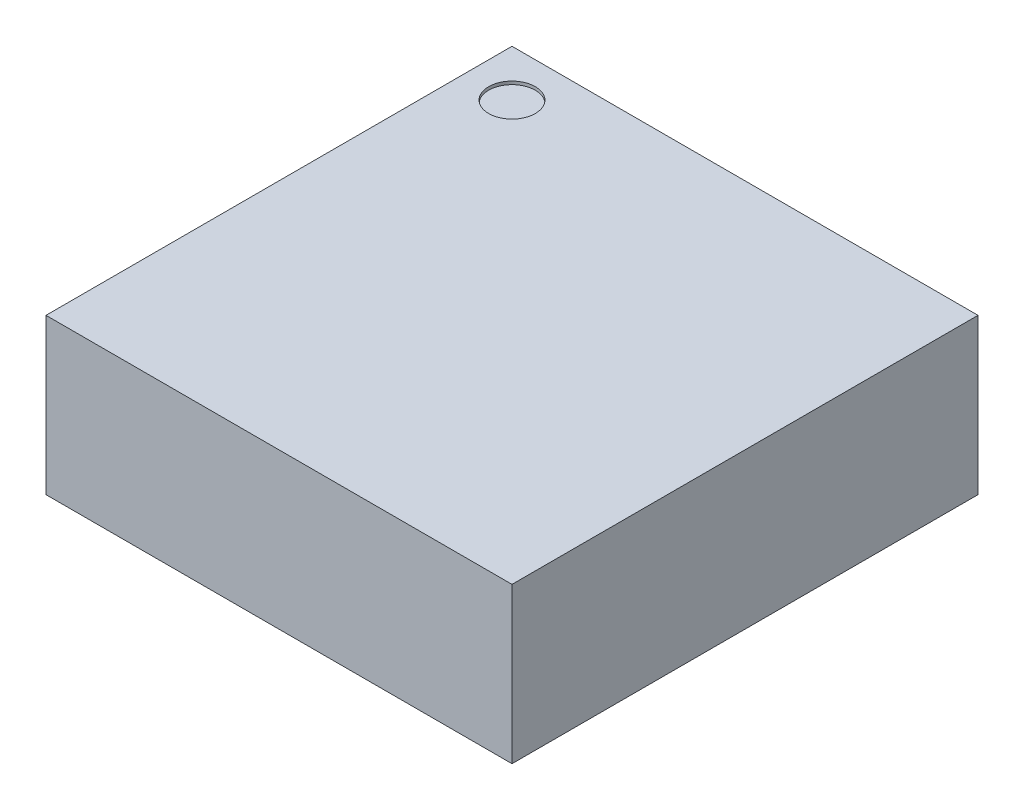
SolidWorks part; units mm, degrees
ref_plane "Front Plane" through (0, 0, 0) normal (0, 0, 1) x (1, 0, 0)
ref_plane "Top Plane" through (0, 0, 0) normal (0, 1, 0) x (1, 0, 0)
ref_plane "Right Plane" through (0, 0, 0) normal (1, 0, 0) x (0, 0, -1)
sketch "Sketch1" plane through (0, 0, 0) normal (0, 1, 0) x (1, 0, 0)
  line L0 (1.5, -1.5) -> (-1.5, 1.5) construction
  line L1 (-1.5, -1.5) -> (1.5, -1.5)
  line L2 (-1.5, -1.5) -> (-1.5, 1.5)
  line L3 (-1.5, 1.5) -> (1.5, 1.5)
  line L4 (1.5, -1.5) -> (1.5, 1.5)
  dimension "D1" = 3
extrude "Boss-Extrude1" add sketch "Sketch1" along normal blind 1
sketch "Sketch2" plane through (0, 0, 0) normal (0, -1, 0) x (1, 0, 0)
  line L0 (1.5, -1.5) -> (-1.5, -1.5) construction
  line L1 (-0.6, 1.39) -> (-0.4, 1.39)
  line L2 (-0.65, 1.34) -> (-0.65, 0.98)
  line L3 (-0.65, 0.98) -> (-0.35, 0.98) construction
  line L4 (-0.35, 1.34) -> (-0.35, 0.98)
  line L5 (-0.1, 1.39) -> (0.1, 1.39)
  line L6 (-0.15, 1.34) -> (-0.15, 0.98)
  line L7 (-0.15, 0.98) -> (0.15, 0.98) construction
  line L8 (0.15, 1.34) -> (0.15, 0.98)
  line L9 (0.4, 1.39) -> (0.6, 1.39)
  line L10 (0.35, 1.34) -> (0.35, 0.98)
  line L11 (0.35, 0.98) -> (0.65, 0.98) construction
  line L12 (0.65, 1.34) -> (0.65, 0.98)
  line L13 (0.35, -0.98) -> (0.65, -0.98) construction
  line L14 (0.35, -0.98) -> (0.35, -1.34)
  line L15 (0.4, -1.39) -> (0.6, -1.39)
  line L16 (0.65, -0.98) -> (0.65, -1.34)
  line L17 (-0.15, -0.98) -> (0.15, -0.98) construction
  line L18 (-0.15, -0.98) -> (-0.15, -1.34)
  line L19 (-0.1, -1.39) -> (0.1, -1.39)
  line L20 (0.15, -0.98) -> (0.15, -1.34)
  line L21 (-0.65, -0.98) -> (-0.35, -0.98) construction
  line L22 (-0.65, -0.98) -> (-0.65, -1.34)
  line L23 (-0.6, -1.39) -> (-0.4, -1.39)
  line L24 (-0.35, -0.98) -> (-0.35, -1.34)
  line L25 (-1.34, 1.15) -> (-0.98, 1.15)
  line L26 (-1.39, 1.1) -> (-1.39, 0.9)
  line L27 (-1.34, 0.85) -> (-0.98, 0.85)
  line L28 (-0.98, 1.15) -> (-0.98, 0.85) construction
  line L29 (-1.34, 0.65) -> (-0.98, 0.65)
  line L30 (-1.39, 0.6) -> (-1.39, 0.4)
  line L31 (-1.34, 0.35) -> (-0.98, 0.35)
  line L32 (-0.98, 0.65) -> (-0.98, 0.35) construction
  line L33 (-1.34, 0.15) -> (-0.98, 0.15)
  line L34 (-1.39, 0.1) -> (-1.39, -0.1)
  line L35 (-1.34, -0.15) -> (-0.98, -0.15)
  line L36 (-0.98, 0.15) -> (-0.98, -0.15) construction
  line L37 (-1.34, -0.35) -> (-0.98, -0.35)
  line L38 (-1.39, -0.4) -> (-1.39, -0.6)
  line L39 (-1.34, -0.65) -> (-0.98, -0.65)
  line L40 (-0.98, -0.35) -> (-0.98, -0.65) construction
  line L41 (-1.34, -0.85) -> (-0.98, -0.85)
  line L42 (-1.39, -0.9) -> (-1.39, -1.1)
  line L43 (-1.34, -1.15) -> (-0.98, -1.15)
  line L44 (-0.98, -0.85) -> (-0.98, -1.15) construction
  line L45 (0.98, -0.35) -> (1.34, -0.35)
  line L46 (0.98, -0.35) -> (0.98, -0.65) construction
  line L47 (0.98, -0.65) -> (1.34, -0.65)
  line L48 (1.39, -0.4) -> (1.39, -0.6)
  line L49 (0.98, -0.85) -> (1.34, -0.85)
  line L50 (0.98, -0.85) -> (0.98, -1.15) construction
  line L51 (0.98, -1.15) -> (1.34, -1.15)
  line L52 (1.39, -0.9) -> (1.39, -1.1)
  line L53 (0.98, 0.15) -> (1.34, 0.15)
  line L54 (0.98, 0.15) -> (0.98, -0.15) construction
  line L55 (0.98, -0.15) -> (1.34, -0.15)
  line L56 (1.39, 0.1) -> (1.39, -0.1)
  line L57 (0.98, 0.65) -> (1.34, 0.65)
  line L58 (0.98, 0.65) -> (0.98, 0.35) construction
  line L59 (0.98, 0.35) -> (1.34, 0.35)
  line L60 (1.39, 0.6) -> (1.39, 0.4)
  line L61 (0.98, 1.15) -> (1.34, 1.15)
  line L62 (0.98, 1.15) -> (0.98, 0.85) construction
  line L63 (0.98, 0.85) -> (1.34, 0.85)
  line L64 (1.39, 1.1) -> (1.39, 0.9)
  line L65 (-0.5, 1.39) -> (-0.5, 1.6137) construction
  line L66 (0, 1.39) -> (0, 1.6766) construction
  line L67 (0.5, 1.39) -> (0.5, 1.6137) construction
  line L68 (1.39, 1) -> (1.9436, 1) construction
  line L69 (1.39, 0.5) -> (1.7859, 0.5) construction
  line L70 (1.39, 0) -> (1.8465, 0) construction
  line L71 (1.39, -1) -> (1.6565, -1) construction
  line L72 (1.39, -0.5) -> (1.7859, -0.5) construction
  line L73 (0.5, -1.39) -> (0.5, -2.1383) construction
  line L74 (0, -1.39) -> (0, -1.3125) construction
  line L75 (-0.5, -1.39) -> (-0.5, -1.6285) construction
  line L76 (-1.39, -1) -> (-1.7444, -1) construction
  line L77 (-1.39, -0.5) -> (-1.9469, -0.5) construction
  line L78 (-1.39, 0) -> (-1.7147, 0) construction
  line L79 (-1.39, 0.5) -> (-1.63, 0.5) construction
  line L80 (-1.39, 1) -> (-1.63, 1) construction
  line L81 (-1.5, 1.5) -> (1.5, 1.5) construction
  line L82 (1.5, 1.5) -> (1.5, -1.5) construction
  line L83 (-1.5, -1.5) -> (-1.5, 1.5) construction
  line L84 (-0.98, -0.85) -> (-0.88, -0.85)
  line L85 (-0.83, -0.9) -> (-0.83, -1)
  line L86 (-0.83, -1) -> (-0.98, -1.15)
  line L87 (-0.83, -0.5) -> (-0.83, -0.85) construction
  arc A0 (-0.65, 0.98) -> (-0.35, 0.98) centre (-0.5, 0.98) ccw
  arc A1 (-0.15, 0.98) -> (0.15, 0.98) centre (0, 0.98) ccw
  arc A2 (0.35, 0.98) -> (0.65, 0.98) centre (0.5, 0.98) ccw
  arc A3 (0.98, 1.15) -> (0.98, 0.85) centre (0.98, 1) ccw
  arc A4 (0.98, 0.35) -> (0.98, 0.65) centre (0.98, 0.5) cw
  arc A5 (0.98, 0.15) -> (0.98, -0.15) centre (0.98, 0) ccw
  arc A6 (0.98, -1.15) -> (0.98, -0.85) centre (0.98, -1) cw
  arc A7 (0.98, -0.35) -> (0.98, -0.65) centre (0.98, -0.5) ccw
  arc A8 (0.35, -0.98) -> (0.65, -0.98) centre (0.5, -0.98) cw
  arc A9 (0.15, -0.98) -> (-0.15, -0.98) centre (0, -0.98) ccw
  arc A10 (-0.35, -0.98) -> (-0.65, -0.98) centre (-0.5, -0.98) ccw
  arc A11 (-0.88, -0.85) -> (-0.83, -0.9) centre (-0.88, -0.9) cw
  arc A12 (-0.98, -0.65) -> (-0.98, -0.35) centre (-0.98, -0.5) ccw
  arc A13 (-0.98, -0.15) -> (-0.98, 0.15) centre (-0.98, 0) ccw
  arc A14 (-0.98, 0.35) -> (-0.98, 0.65) centre (-0.98, 0.5) ccw
  arc A15 (-0.98, 1.15) -> (-0.98, 0.85) centre (-0.98, 1) cw
  arc A16 (-0.65, 1.34) -> (-0.6, 1.39) centre (-0.6, 1.34) cw
  arc A17 (-0.4, 1.39) -> (-0.35, 1.34) centre (-0.4, 1.34) cw
  arc A18 (-0.15, 1.34) -> (-0.1, 1.39) centre (-0.1, 1.34) cw
  arc A19 (0.15, 1.34) -> (0.1, 1.39) centre (0.1, 1.34) ccw
  arc A20 (0.35, 1.34) -> (0.4, 1.39) centre (0.4, 1.34) cw
  arc A21 (0.6, 1.39) -> (0.65, 1.34) centre (0.6, 1.34) cw
  arc A22 (1.34, 1.15) -> (1.39, 1.1) centre (1.34, 1.1) cw
  arc A23 (1.39, 0.9) -> (1.34, 0.85) centre (1.34, 0.9) cw
  arc A24 (1.34, 0.65) -> (1.39, 0.6) centre (1.34, 0.6) cw
  arc A25 (1.39, 0.4) -> (1.34, 0.35) centre (1.34, 0.4) cw
  arc A26 (1.34, 0.15) -> (1.39, 0.1) centre (1.34, 0.1) cw
  arc A27 (1.39, -0.1) -> (1.34, -0.15) centre (1.34, -0.1) cw
  arc A28 (1.34, -0.35) -> (1.39, -0.4) centre (1.34, -0.4) cw
  arc A29 (1.34, -0.65) -> (1.39, -0.6) centre (1.34, -0.6) ccw
  arc A30 (1.34, -0.85) -> (1.39, -0.9) centre (1.34, -0.9) cw
  arc A31 (1.39, -1.1) -> (1.34, -1.15) centre (1.34, -1.1) cw
  arc A32 (0.65, -1.34) -> (0.6, -1.39) centre (0.6, -1.34) cw
  arc A33 (0.4, -1.39) -> (0.35, -1.34) centre (0.4, -1.34) cw
  arc A34 (0.15, -1.34) -> (0.1, -1.39) centre (0.1, -1.34) cw
  arc A35 (-0.15, -1.34) -> (-0.1, -1.39) centre (-0.1, -1.34) ccw
  arc A36 (-0.35, -1.34) -> (-0.4, -1.39) centre (-0.4, -1.34) cw
  arc A37 (-0.6, -1.39) -> (-0.65, -1.34) centre (-0.6, -1.34) cw
  arc A38 (-1.34, -1.15) -> (-1.39, -1.1) centre (-1.34, -1.1) cw
  arc A39 (-1.39, -0.9) -> (-1.34, -0.85) centre (-1.34, -0.9) cw
  arc A40 (-1.34, -0.65) -> (-1.39, -0.6) centre (-1.34, -0.6) cw
  arc A41 (-1.39, -0.4) -> (-1.34, -0.35) centre (-1.34, -0.4) cw
  arc A42 (-1.34, -0.15) -> (-1.39, -0.1) centre (-1.34, -0.1) cw
  arc A43 (-1.39, 0.1) -> (-1.34, 0.15) centre (-1.34, 0.1) cw
  arc A44 (-1.34, 0.35) -> (-1.39, 0.4) centre (-1.34, 0.4) cw
  arc A45 (-1.39, 0.6) -> (-1.34, 0.65) centre (-1.34, 0.6) cw
  arc A46 (-1.34, 0.85) -> (-1.39, 0.9) centre (-1.34, 0.9) cw
  arc A47 (-1.34, 1.15) -> (-1.39, 1.1) centre (-1.34, 1.1) ccw
  point P112 (0.5, -0.83)
  point P115 (0.83, 1)
  point P116 (0.5, 0.83)
  point P118 (-0.83, 1)
  point P190 (-0.83, -0.5)
  dimension "D19" = 0.05
  dimension "D20" = 0.05
  dimension "D1" = 0.5
  dimension "D2" = 0.5
  dimension "D3" = 0.5
  dimension "D4" = 0.5
  dimension "D5" = 0.3
  dimension "D6" = 0.56
  dimension "D7" = 0.5
  dimension "D8" = 0.5
  dimension "D9" = 0.5
  dimension "D10" = 0.5
  dimension "D11" = 0.5
  dimension "D12" = 0.5
  dimension "D13" = 0.5
  dimension "D14" = 0.5
  dimension "D15" = 0.67
  dimension "D16" = 0.67
  dimension "D17" = 0.67
  dimension "D18" = 0.67
  dimension "D21" = 45
extrude "Boss-Extrude2" add sketch "Sketch2" along normal blind 0.05
sketch "Sketch3" plane through (0, 1, 0) normal (0, 1, 0) x (1, 0, 0)
  line L0 (-1.5, 1.5) -> (-1.5, -1.5) construction
  line L1 (1.5, 1.5) -> (-1.5, 1.5) construction
  circle A0 centre (-1.2, 1.2) radius 0.15
  dimension "D1" = 0.3
  dimension "D2" = 0.3
  dimension "D3" = 0.3
extrude "Cut-Extrude1" cut sketch "Sketch3" against normal blind 0.02
